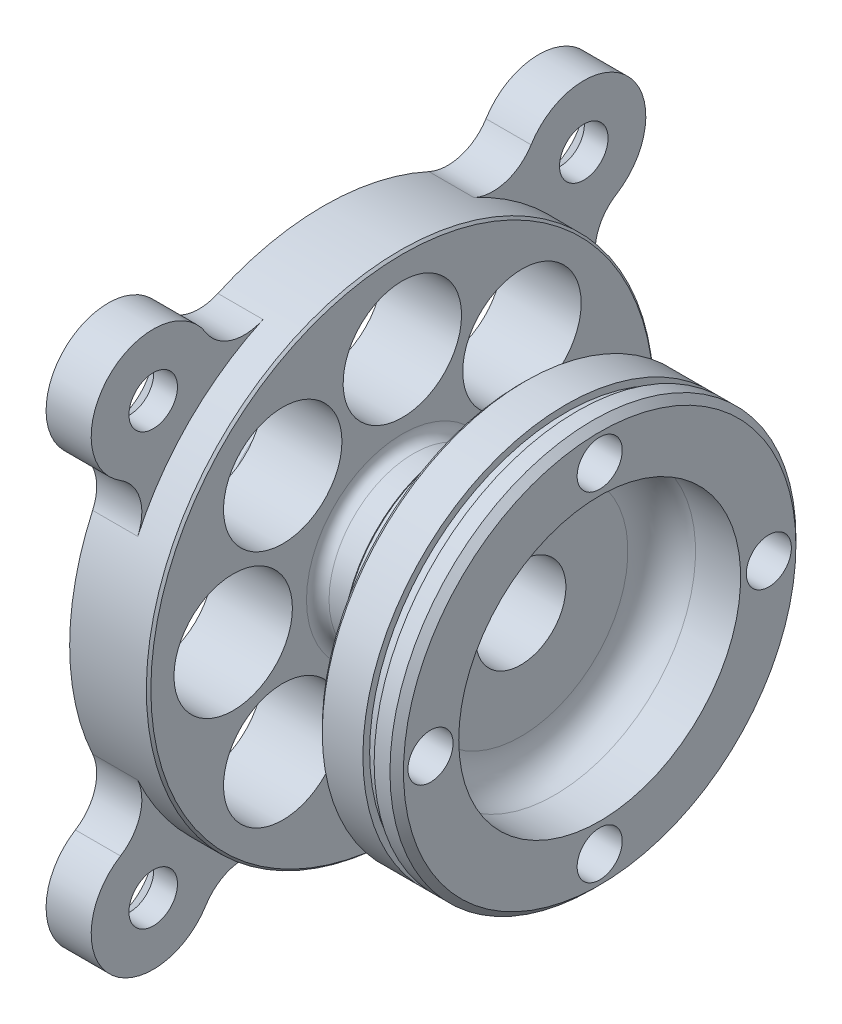
SolidWorks part; units mm, degrees
material "7075-T6 (SN)"
ref_plane "Ebene vorne" through (0, 0, 0) normal (0, 0, 1) x (1, 0, 0)
ref_plane "Ebene oben" through (0, 0, 0) normal (0, 1, 0) x (1, 0, 0)
ref_plane "Ebene rechts" through (0, 0, 0) normal (1, 0, 0) x (0, 0, -1)
sketch "Skizze1" plane through (0, 0, 0) normal (0, 0, 1) x (1, 0, 0)
  line L0 (11, 24) -> (11, 0)
  line L1 (28.5, 14.5) -> (32.5, 14.5)
  line L2 (11, 0) -> (15, 0)
  line L3 (7, 25) -> (7, 24)
  line L4 (7, 25) -> (0, 25)
  line L5 (0, 25) -> (0, 28.5)
  line L6 (28.5, 14.5) -> (28.5, 22)
  line L7 (23, 25) -> (18, 25)
  line L8 (15, 0) -> (15, 10)
  line L9 (23, 25) -> (23, 22)
  line L10 (-20.5313, 32.5) -> (49.1014, 32.5)
  line L11 (15, 10) -> (18, 10)
  line L12 (18, 10) -> (18, 25)
  line L13 (23, 22) -> (28.5, 22)
  line L14 (7, 24) -> (11, 24)
  line L18 (32.5, 14.5) -> (32.5, 15.1)
  line L19 (32.5, 15.1) -> (33.5, 15.1)
  line L20 (28.5, 28.5) -> (0, 28.5)
  line L21 (33.5, 15.1) -> (33.5, 14.5)
  line L22 (33.5, 14.5) -> (35.5, 14.5)
  line L23 (28.5, 28.5) -> (28.5, 23)
  line L24 (31.5, 20) -> (35.5, 20)
  line L25 (35.5, 14.5) -> (35.5, 20)
  arc A0 (31.5, 20) -> (28.5, 23) centre (31.5, 23) cw
  dimension "D26" = 3
  dimension "D1" = 7
  dimension "D2" = 7.5
  dimension "D3" = 0
  dimension "D4" = 7.5
  dimension "D5" = 24.5
  dimension "D6" = 18
  dimension "D7" = 35.5
  dimension "D8" = 4
  dimension "D9" = 8.5
  dimension "D10" = 32.5
  dimension "D11" = 7
  dimension "D12" = 0
  dimension "D13" = 4
  dimension "D14" = 10.5
  dimension "D15" = 23
  dimension "D16" = 22.5
  dimension "D17" = 4
  dimension "D18" = 3
  dimension "D21" = 1
  dimension "D22" = 2
  dimension "D23" = 0.6
  dimension "D24" = 12.5
  dimension "D25" = 7
revolve "Rotation1" add sketch "Skizze1" angle 360 about L10
sketch "Skizze8" plane through (35.5, 0, 0) normal (1, 0, 0) x (0, 0, -1)
  line L0 (0, 32.5601) -> (8.9103, 54.0713)
  line L1 (0, 32.5601) -> (0, 40.8674)
  line L2 (0, 32.5601) -> (17.3191, 49.8792)
  line L3 (0, 32.5601) -> (24.8892, 42.8695)
  circle A0 centre (0, 32.5601) radius 15
  point P6 (5.7403, 46.4183)
  point P7 (10.6066, 43.1667)
  point P8 (13.8582, 38.3003)
  point P9 (13.8582, 26.8198)
  point P10 (10.6066, 21.9535)
  point P11 (5.7403, 18.7019)
  point P12 (-5.7403, 18.7019)
  point P13 (-10.6066, 21.9535)
  point P14 (-13.8582, 26.8198)
  point P15 (-13.8582, 38.3003)
  point P16 (-10.6066, 43.1667)
  point P17 (-5.7403, 46.4183)
  dimension "D1" = 22.5
  dimension "D2" = 22.5
  dimension "D3" = 22.5
fillet "Verrundung1" radius 1 1 edges at (11, 32.5, 8.5)
fillet "Verrundung2" radius 1 2 edges at (23, 32.5, 7.5) (18, 32.5, 7.5)
chamfer "Fase1" distance 0.2 angle 45 2 edges at (18, 32.5, 22.5) (23, 32.5, 10.5)
sketch "Skizze9" plane through (11, 0, 0) normal (-1, 0, 0) x (0, 0, 1)
  line L0 (-15, 32.5) -> (0, 32.5)
  line L1 (0, 32.5) -> (15, 32.5)
  line L2 (0, 47.5) -> (0, 17.5)
  circle A0 centre (0, 32.5) radius 15
  dimension "D1" = 30
sketch "Skizze18" plane through (11, 0, 0) normal (-1, 0, 0) x (0, 0, 1)
  circle A0 centre (0, 32.5) radius 15
  circle A1 centre (0, 32.5) radius 7.5 construction
  circle A2 centre (15, 32.5) radius 5.25
  dimension "D1" = 30
  dimension "D2" = 10.5
chamfer "Fase4" distance 0.6 angle 45 1 edges at (35.5, 32.5, 18)
ref_plane "Ebene3" through (0, 23.6746, -23.6746) normal (0, 0.7071, -0.7071) x (-1, 0, 0)
extrude "Schnitt-Linear austragen7" cut sketch "Skizze18" against normal blind 10 contours A2
pattern_circular "Kreismuster1" count 8 over 360 about axis through (0, 32.5, 0) along (1, 0, 0) of "Schnitt-Linear austragen7"
chamfer "Fase5" distance 0.4 angle 45 1 edges at (28.5, 32.5, 18)
sketch "Skizze26" plane through (11, 0, 0) normal (-1, 0, 0) x (0, 0, 1)
  circle A0 centre (-15, 32.5) radius 5.25
  circle A1 centre (0, 17.5) radius 5.25
  circle A2 centre (0, 17.5) radius 5.25 construction
  circle A3 centre (-15, 32.5) radius 5.25 construction
  circle A4 centre (0, 47.5) radius 5.25
  circle A5 centre (15, 32.5) radius 5.25
  circle A6 centre (15, 32.5) radius 5.25 construction
  circle A7 centre (0, 47.5) radius 5.25 construction
hole_wizard "Ø4.0 (4) Durchmesser Bohrung2" positions "3D-Skizze2" profile "Skizze29" hole size "Ø4.0" standard "DIN" end condition through all
sketch3d "3D-Skizze2"
  point P0 (11, 47.5, 0)
  point P3 (11, 17.5, 0)
  point P6 (11, 32.5, 15)
  point P9 (11, 32.5, -15)
sketch "Skizze29" plane through (11, 47.5, 0) normal (0, 1, 0) x (0, 0, 1)
  line L0 (0, 0) -> (0, 24.5)
  line L1 (0, 24.5) -> (2, 24.5)
  line L2 (2, 24.5) -> (2, 0)
  line L5 (2, 0) -> (0, 0)
  line L11 (0, -6.35) -> (0, 107.95) construction
  dimension "Bohrerdurchmesser" = 4
  dimension "Bohrungstiefe" = 24.5
chamfer "Fase6" distance 0.2 angle 45 2 edges at (0, 32.5, 7.5) (7, 32.5, 8.5)
fillet "Verrundung3" radius 1 1 edges at (28.5, 32.5, 10.5)
sketch "Skizze30" plane through (11, 0, 0) normal (-1, 0, 0) x (0, 0, 1)
  line L0 (0, 32.5) -> (19.0919, 51.5919)
  line L1 (-15, 32.5) -> (-52.3523, 32.5)
  line L2 (-19.0919, 51.5919) -> (0, 32.5)
  line L3 (-19.0919, 13.4081) -> (0, 32.5)
  line L4 (0, 32.5) -> (19.0919, 13.4081)
  arc A0 (9.356, 52.9625) -> (20.4625, 41.856) centre (0, 32.5) ccw
  arc A1 (21.9915, 46.9183) -> (14.4183, 54.4915) centre (19.0919, 51.5919) ccw
  circle A2 centre (0, 32.5) radius 32.5 construction
  arc A3 (20.4625, 41.856) -> (21.9915, 46.9183) centre (24.1003, 43.5193) cw
  arc A4 (14.4183, 54.4915) -> (9.356, 52.9625) centre (11.0193, 56.6003) cw
  arc A5 (14.4183, 10.5085) -> (21.9915, 18.0817) centre (19.0919, 13.4081) ccw
  arc A6 (21.9915, 18.0817) -> (20.4625, 23.144) centre (24.1003, 21.4807) cw
  arc A7 (9.356, 12.0375) -> (14.4183, 10.5085) centre (11.0193, 8.3997) cw
  arc A8 (-21.9915, 18.0817) -> (-14.4183, 10.5085) centre (-19.0919, 13.4081) ccw
  arc A9 (-14.4183, 10.5085) -> (-9.356, 12.0375) centre (-11.0193, 8.3997) cw
  arc A10 (-20.4625, 23.144) -> (-21.9915, 18.0817) centre (-24.1003, 21.4807) cw
  arc A11 (-14.4183, 54.4915) -> (-21.9915, 46.9183) centre (-19.0919, 51.5919) ccw
  arc A12 (-21.9915, 46.9183) -> (-20.4625, 41.856) centre (-24.1003, 43.5193) cw
  arc A13 (-9.356, 52.9625) -> (-14.4183, 54.4915) centre (-11.0193, 56.6003) cw
  circle A14 centre (0, 32.5) radius 37.5159
  circle M10 centre (0, 32.5) radius 32.5
  dimension "D1" = 45
  dimension "D2" = 5.5
  dimension "D4" = 4
  dimension "D3" = 135
  dimension "D5" = 4
extrude "Schnitt-Linear austragen9" cut sketch "Skizze30" against normal through all contours A13 A0 A4 A1 A11 M10 | A12 A11 L1 A0 M10 | A10 A0 L1 A8 M10 | A9 A8 A5 A7 A0 M10 | A6 A5 A1 A3 A0 M10
hole_wizard "Formsenkung für M4 Senkschraube mit Innensechskant1" positions "3D-Skizze3" profile "Skizze34" countersink size "M4" standard "DIN" end condition through all
sketch3d "3D-Skizze3"
  line L0 (15, 51.5919, -19.0919) -> (11, 51.5919, -19.0919) construction
  line L1 (15, 13.4081, -19.0919) -> (11, 13.4081, -19.0919) construction
  line L2 (15, 13.4081, 19.0919) -> (11, 13.4081, 19.0919) construction
  line L3 (15, 51.5919, 19.0919) -> (11, 51.5919, 19.0919) construction
  point P0 (11, 51.5919, -19.0919)
  point P4 (11, 13.4081, -19.0919)
  point P8 (11, 13.4081, 19.0919)
  point P12 (11, 51.5919, 19.0919)
sketch "Skizze34" plane through (11, 51.5919, -19.0919) normal (0, 1, 0) x (0, 0, 1)
  line L0 (0, 0) -> (0, 24.5)
  line L1 (0, 24.5) -> (2.15, 24.5)
  line L2 (2.15, 24.5) -> (2.15, 1.9)
  line L3 (2.15, 1.9) -> (4.05, 0)
  line L5 (4.05, 0) -> (0, 0)
  line L6 (-2.15, 1.9) -> (-4.05, 0) construction
  line L11 (0, -6.35) -> (0, 107.95) construction
  dimension "Bohrerdurchmesser" = 4.3
  dimension "Bohrungstiefe" = 24.5
  dimension "Senkdurchmesser (Oben)" = 8.1
  dimension "Senkwinkel (Oben)" = 90
ref_plane "Ebene4" through (0, 0, -10.5) normal (0, 0, 1) x (1, 0, 0)
sketch "Skizze37" plane through (0, 0, 0) normal (-1, 0, 0) x (0, 0, 1)
  line L0 (0, 32.5) -> (-29.3207, 32.5)
sketch "Skizze36" plane through (0, 0, -10.5) normal (0, 0, 1) x (1, 0, 0)
  line L0 (25.4, 32.5173) -> (-12.1977, 32.5173)
  line L1 (23, 42.8) -> (23, 22.2) construction
  point P0 (25.4, 32.5173)
  dimension "D1" = 2.4
sketch "Skizze49" plane through (0, 0, -10.5) normal (0, 0, 1) x (1, 0, 0)
  circle A0 centre (25.4, 32.5173) radius 13.3345
